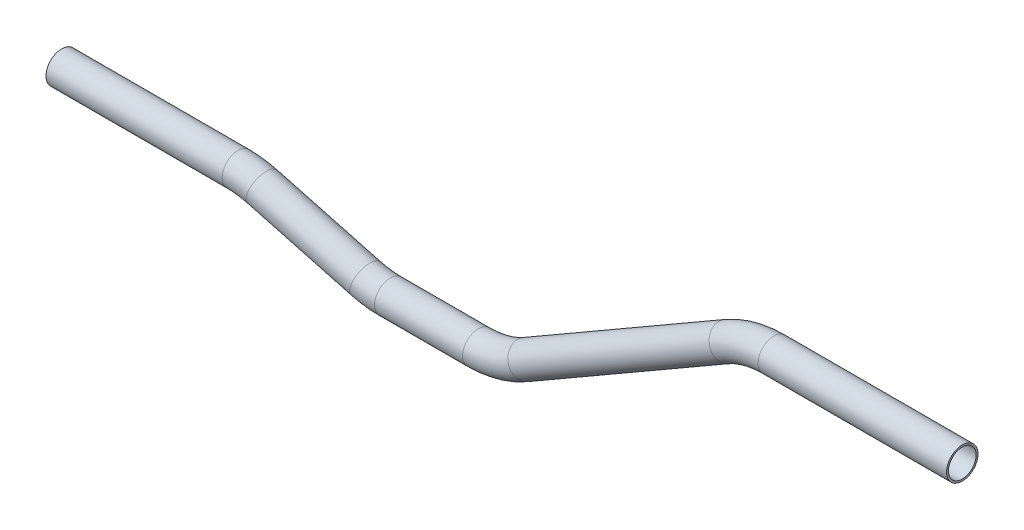
SolidWorks part; units mm, degrees
material "6061-T6 (SS)"
ref_plane "Front Plane" through (0, 0, 0) normal (0, 0, 1) x (1, 0, 0)
ref_plane "Top Plane" through (0, 0, 0) normal (0, 1, 0) x (1, 0, 0)
ref_plane "Right Plane" through (0, 0, 0) normal (1, 0, 0) x (0, 0, -1)
sketch "Sketch1" plane through (0, 0, 0) normal (0, 0, 1) x (1, 0, 0)
  line L0 (-17.5848, 20.651) -> (53.5992, 20.651)
  line L1 (63.4602, 19.3527) -> (105.2926, 8.1438)
  line L2 (115.1536, 6.8456) -> (150.7288, 6.8456)
  line L3 (-17.5848, 20.651) -> (53.5992, 20.651) construction
  line L4 (53.5992, 20.651) -> (131.818, 20.651) construction
  line L5 (105.2926, 8.1438) -> (63.4602, 19.3527) construction
  line L6 (63.4602, 19.3527) -> (-0.3074, 36.4392) construction
  line L7 (63.4602, 19.3527) -> (105.2926, 8.1438) construction
  line L8 (105.2926, 8.1438) -> (149.2188, -3.6262) construction
  line L9 (150.7288, 6.8456) -> (115.1536, 6.8456) construction
  line L10 (115.1536, 6.8456) -> (63.6317, 6.8456) construction
  line L11 (169.7788, 11.95) -> (251.0832, 58.8911)
  line L12 (270.1332, 63.9956) -> (346.2843, 63.9956)
  line L13 (150.7288, 6.8456) -> (234.8088, 6.8456) construction
  line L14 (251.0832, 58.8911) -> (169.7788, 11.95) construction
  line L15 (169.7788, 11.95) -> (93.8076, -31.912) construction
  line L16 (346.2843, 63.9956) -> (270.1332, 63.9956) construction
  line L17 (270.1332, 63.9956) -> (197.0706, 63.9956) construction
  line L18 (169.7788, 11.95) -> (251.0832, 58.8911) construction
  line L19 (251.0832, 58.8911) -> (282.5672, 77.0684) construction
  arc A0 (53.5992, 20.651) -> (63.4602, 19.3527) centre (53.5992, -17.449) cw
  arc A1 (105.2926, 8.1438) -> (115.1536, 6.8456) centre (115.1536, 44.9456) ccw
  arc A2 (150.7288, 6.8456) -> (169.7788, 11.95) centre (150.7288, 44.9456) ccw
  arc A3 (251.0832, 58.8911) -> (270.1332, 63.9956) centre (270.1332, 25.8956) cw
  point P7 (58.6152, 20.651)
  point P13 (110.1376, 6.8456)
  point P22 (259.9243, 63.9956)
  point P25 (160.9376, 6.8456)
  dimension "D1" = 38.1
  dimension "D2" = 38.1
  dimension "D6" = 38.1
  dimension "D8" = 38.1
  dimension "D3" = 15
  dimension "D4" = 15
  dimension "D5" = 76.2
  dimension "D7" = 53.34
  dimension "D9" = 50.8
  dimension "D10" = 114.3
  dimension "D11" = 30
  dimension "D12" = 30
  dimension "D13" = 86.36
ref_plane "Plane1" through (-17.5848, 20.651, 0) normal (1, 0, 0) x (0, 0, -1)
sketch "Sketch2" plane through (-17.5848, 20.651, 0) normal (1, 0, 0) x (0, 0, -1)
  circle A0 centre (0, 0) radius 6.35
  circle A1 centre (0, 0) radius 5.588
  dimension "D1" = 11.176
  dimension "D2" = 12.7
sweep "Sweep1" add profiles "Sketch2" path "Sketch1"
